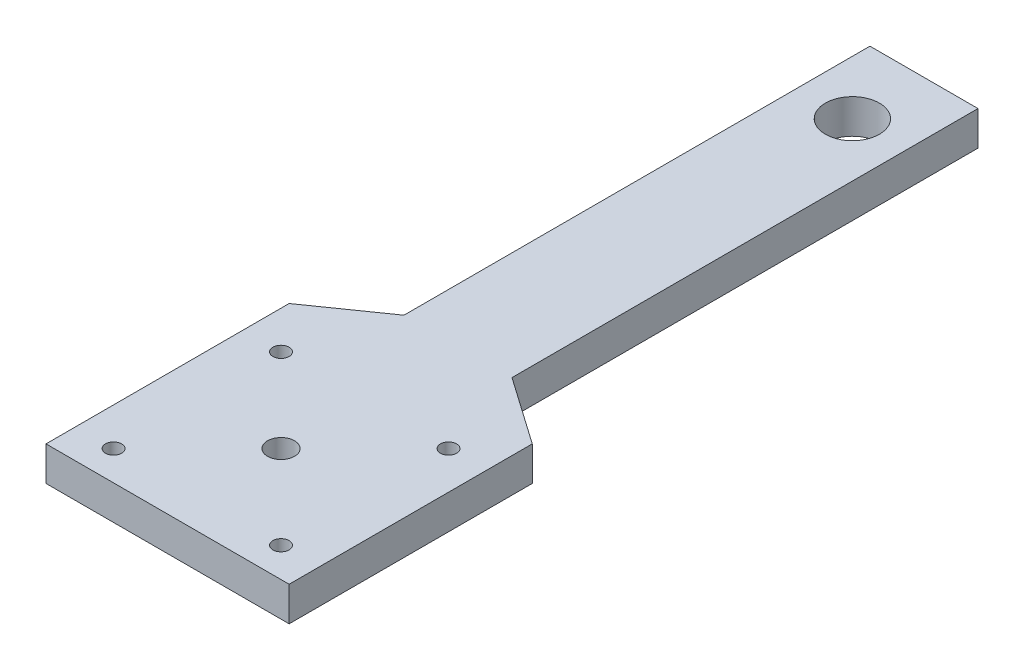
SolidWorks part; units mm, degrees
ref_plane "Front Plane" through (0, 0, 0) normal (0, 0, 1) x (1, 0, 0)
ref_plane "Top Plane" through (0, 0, 0) normal (0, 1, 0) x (1, 0, 0)
ref_plane "Right Plane" through (0, 0, 0) normal (1, 0, 0) x (0, 0, -1)
sketch "Sketch1" plane through (0, 0, 0) normal (0, 1, 0) x (1, 0, 0)
  line L0 (0, -63.375) -> (0, 63.375) construction
  line L2 (-10, -9.6224) -> (-10, 76.625)
  line L3 (-10, 76.625) -> (10, 76.625)
  line L5 (0, -63.375) -> (-22.5, -63.375)
  line L6 (0, -63.375) -> (22.5, -63.375)
  line L7 (-22.5, -63.375) -> (-22.5, -18.375)
  line L8 (22.5, -63.375) -> (22.5, -18.375)
  line L9 (-22.5, -18.375) -> (-10, -9.6224)
  line L10 (10, -9.6224) -> (10, 76.625)
  line L11 (22.5, -18.375) -> (10, -9.6224)
  line L12 (0, -63.375) -> (0, -33.7457) construction
  line L13 (-15.5, -26.875) -> (15.5, -26.875) construction
  line L14 (0, -63.375) -> (0, -42.375) construction
  line L15 (15.5, -26.875) -> (15.5, -57.875) construction
  line L16 (15.5, -57.875) -> (-15.5, -57.875) construction
  line L17 (-15.5, -57.875) -> (-15.5, -26.875) construction
  line L18 (0, -26.875) -> (0, -57.875) construction
  circle A0 centre (0, 63.375) radius 5
  circle A5 centre (-15.5, -26.875) radius 1.5
  circle A6 centre (15.5, -26.875) radius 1.5
  circle A7 centre (15.5, -57.875) radius 1.5
  circle A8 centre (-15.5, -57.875) radius 1.5
  circle A9 centre (0, -42.375) radius 2.5
  point P3 (0, 0)
  point P12 (0, 0)
  point P33 (0, -26.875)
  point P34 (-15.5, -42.375)
  point P37 (0, -42.375)
  dimension "D3" = 10
  dimension "D4" = 13.25
  dimension "D7" = 3
  dimension "D2" = 5
  dimension "D13" = 26.875
  dimension "D1" = 20
  dimension "D5" = 140
  dimension "D6" = 45
  dimension "D8" = 31
  dimension "D9" = 31
  dimension "D10" = 45
  dimension "D11" = 125
  dimension "D12" = 125
extrude "Boss-Extrude1" add sketch "Sketch1" along normal blind 6.35
